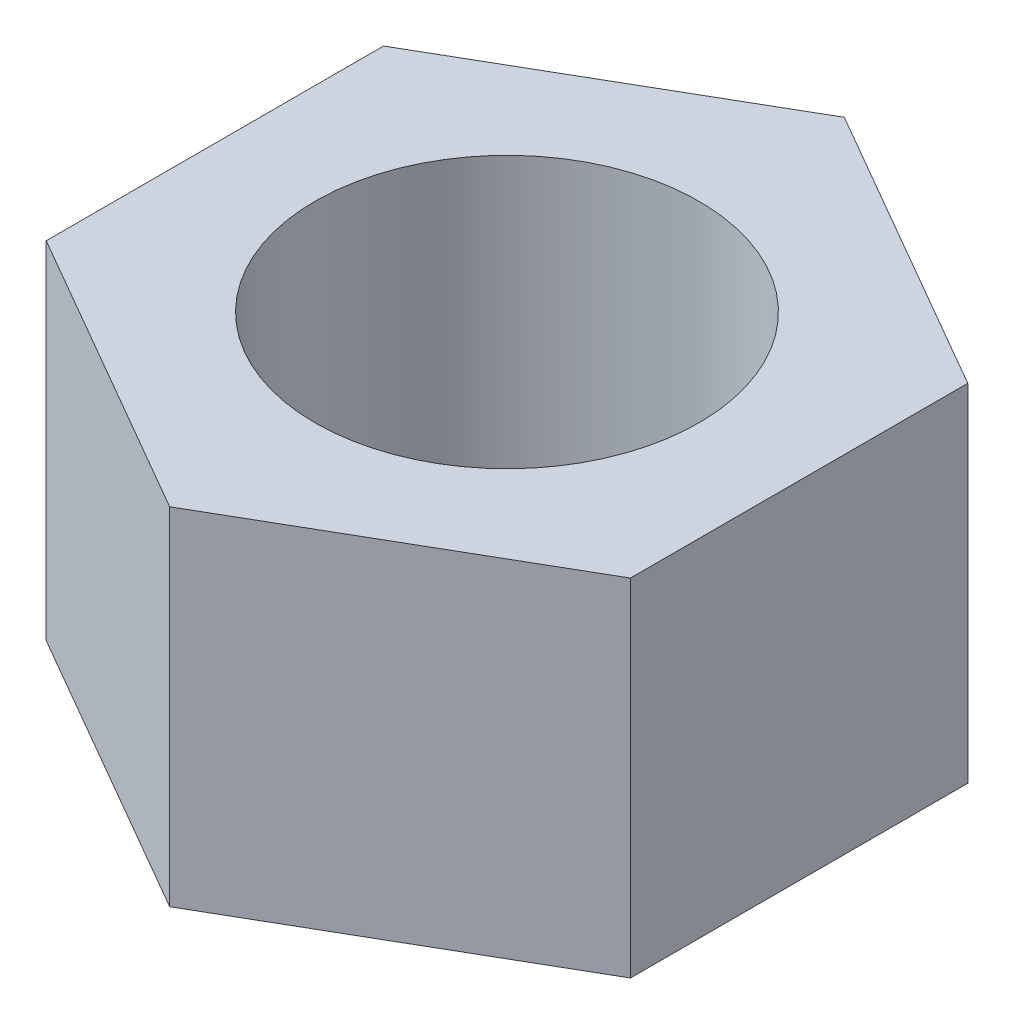
SolidWorks part; units mm, degrees
material "Chrome Stainless Steel"
ref_plane "Front Plane" through (0, 0, 0) normal (0, 0, 1) x (1, 0, 0)
ref_plane "Top Plane" through (0, 0, 0) normal (0, 1, 0) x (1, 0, 0)
ref_plane "Right Plane" through (0, 0, 0) normal (1, 0, 0) x (0, 0, -1)
sketch "Sketch1" plane through (0, 0, 0) normal (0, 1, 0) x (1, 0, 0)
  line L1 (0, 8.0829) -> (-7, 4.0415)
  line L2 (-7, 4.0415) -> (-7, -4.0415)
  line L3 (-7, -4.0415) -> (0, -8.0829)
  line L4 (0, -8.0829) -> (7, -4.0415)
  line L5 (7, -4.0415) -> (7, 4.0415)
  line L6 (7, 4.0415) -> (0, 8.0829)
  circle A0 centre (0, 0) radius 7 construction
extrude "Boss-Extrude1" add sketch "Sketch1" along normal blind 8.3
sketch "Sketch2" plane through (0, 8.3, 0) normal (0, 1, 0) x (1, 0, 0)
  circle A0 centre (0, 0) radius 4.6
extrude "Cut-Extrude1" cut sketch "Sketch2" against normal through all
